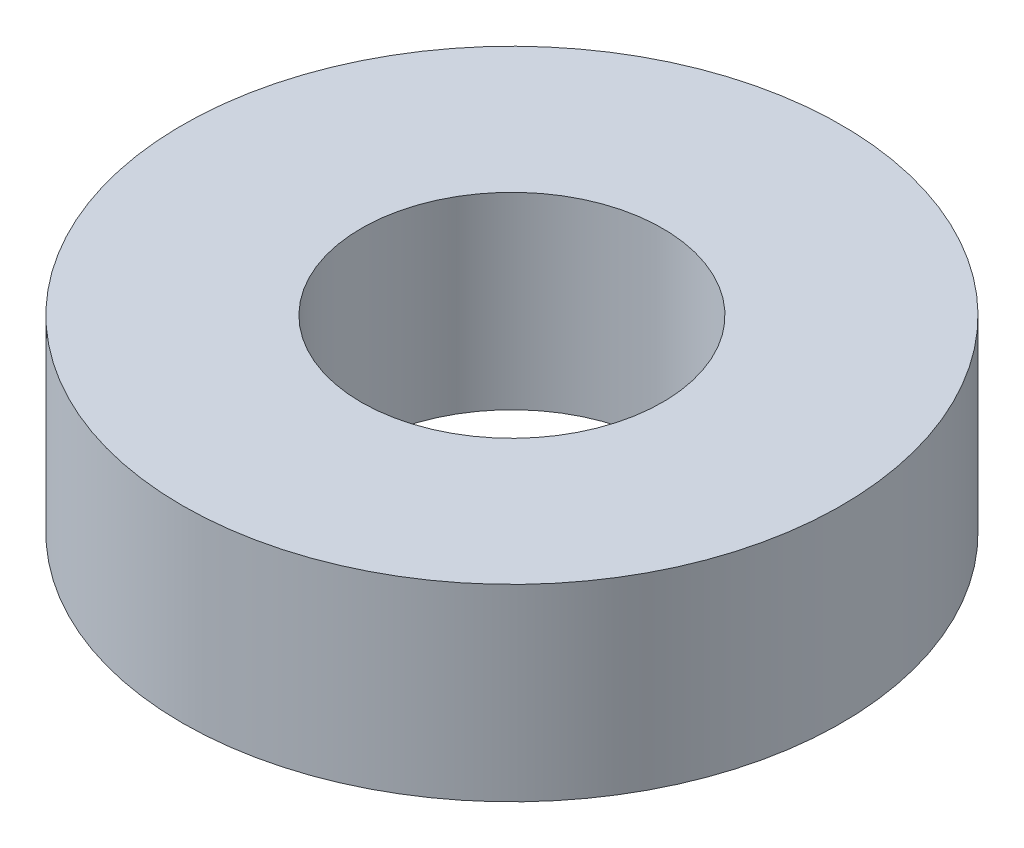
SolidWorks part; units mm, degrees
ref_plane "Front Plane" through (0, 0, 0) normal (0, 0, 1) x (1, 0, 0)
ref_plane "Top Plane" through (0, 0, 0) normal (0, 1, 0) x (1, 0, 0)
ref_plane "Right Plane" through (0, 0, 0) normal (1, 0, 0) x (0, 0, -1)
sketch "Sketch1" plane through (0, 0, 0) normal (0, 1, 0) x (1, 0, 0)
  circle A0 centre (0, 0) radius 1.6
  circle A1 centre (0, 0) radius 3.5
  dimension "D1" = 3.2
  dimension "D2" = 7
extrude "Boss-Extrude1" add sketch "Sketch1" along normal blind 2
